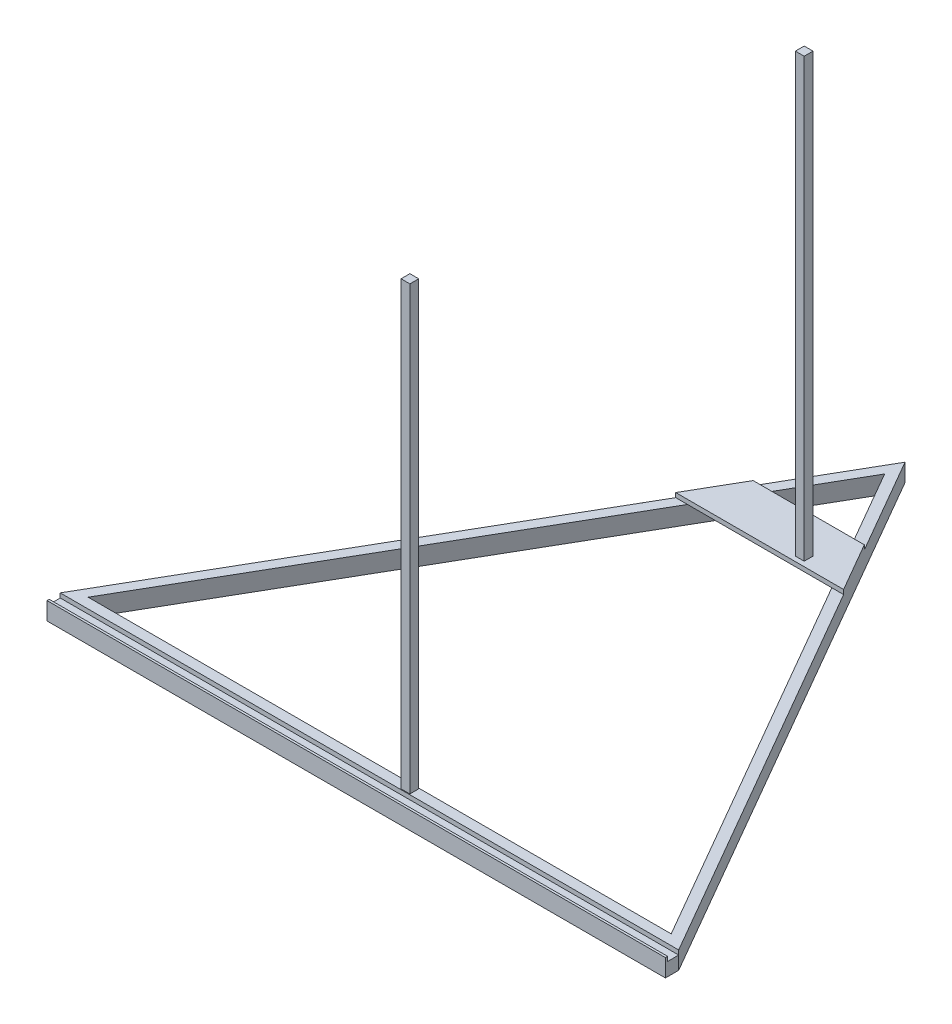
SolidWorks part; units mm, degrees
ref_plane "Front Plane" through (0, 0, 0) normal (0, 0, 1) x (1, 0, 0)
ref_plane "Top Plane" through (0, 0, 0) normal (0, 1, 0) x (1, 0, 0)
ref_plane "Right Plane" through (0, 0, 0) normal (1, 0, 0) x (0, 0, -1)
sketch "Sketch1" plane through (0, 0, 0) normal (0, 1, 0) x (1, 0, 0)
  line L1 (0, 404.1452) -> (-350, -202.0726)
  line L2 (-350, -202.0726) -> (350, -202.0726)
  line L3 (350, -202.0726) -> (0, 404.1452)
  line L4 (0, 381.0512) -> (-330, -190.5256)
  line L5 (-330, -190.5256) -> (330, -190.5256)
  line L6 (330, -190.5256) -> (0, 381.0512)
  circle A0 centre (0, 0) radius 202.0726 construction
  circle A1 centre (0, 0) radius 190.5256 construction
extrude "Boss-Extrude1" add sketch "Sketch1" along normal blind 20
sketch "Sketch2" plane through (0, 0, 0) normal (0, 1, 0) x (1, 0, 0)
  line L1 (-350, -202.0726) -> (350, -202.0726)
  line L2 (-350, -202.0726) -> (-350, -217.0726)
  line L3 (-350, -217.0726) -> (350, -217.0726)
  line L4 (350, -202.0726) -> (350, -217.0726)
extrude "Boss-Extrude2" add sketch "Sketch2" along normal blind 20 contours L3 L4 L1 L2
sketch "Sketch4" plane through (0, 20, 0) normal (0, 1, 0) x (1, 0, 0)
  line L2 (350, -202.0726) -> (-350, -202.0726)
  line L3 (350, -202.0726) -> (350, -214.5726)
  line L4 (350, -214.5726) -> (-350, -214.5726)
  line L6 (-350, -202.0726) -> (-350, -214.5726)
sketch "Sketch6" plane through (0, 20, 0) normal (0, 1, 0) x (1, 0, 0)
  line L1 (35, -201.3) -> (45, -201.3)
  line L2 (45, -201.3) -> (45, -191.3)
  line L3 (45, -191.3) -> (35, -191.3)
  line L4 (35, -191.3) -> (35, -201.3)
  circle A0 centre (40, -196.3) radius 5 construction
extrude "Boss-Extrude3" add sketch "Sketch6" along normal blind 500
sketch "Sketch7" plane through (0, 20, 0) normal (0, 1, 0) x (1, 0, 0)
  line L0 (62.9421, 295.1263) -> (-62.9421, 295.1263)
  line L1 (350, -202.0726) -> (0, 404.1452) construction
  line L2 (0, 404.1452) -> (-350, -202.0726) construction
  line L3 (-62.9421, 295.1263) -> (-95, 239.6004)
  line L4 (-95, 239.6004) -> (95, 239.6004)
  line L5 (95, 239.6004) -> (62.9421, 295.1263)
extrude "Boss-Extrude4" add sketch "Sketch7" along normal blind 5
sketch "Sketch8" plane through (0, 25, 0) normal (0, 1, 0) x (1, 0, 0)
  line L1 (45, 255) -> (35, 255)
  line L2 (35, 255) -> (35, 245)
  line L3 (35, 245) -> (45, 245)
  line L4 (45, 245) -> (45, 255)
  circle A0 centre (40, 250) radius 5 construction
extrude "Boss-Extrude5" add sketch "Sketch8" along normal blind 495 contours L3 L4 L1 L2
extrude "Cut-Extrude2" cut sketch "Sketch4" against normal blind 5
